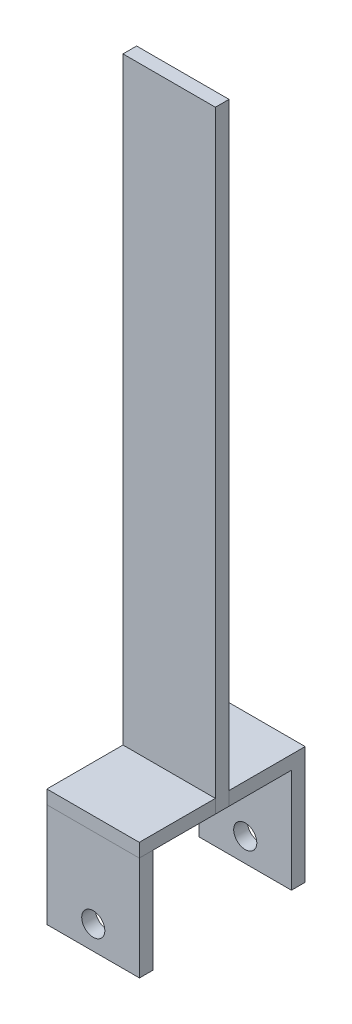
SolidWorks part; units mm, degrees
material "6063-T6"
ref_plane "Front Plane" through (0, 0, 0) normal (0, 0, 1) x (1, 0, 0)
ref_plane "Top Plane" through (0, 0, 0) normal (0, 1, 0) x (1, 0, 0)
ref_plane "Right Plane" through (0, 0, 0) normal (1, 0, 0) x (0, 0, -1)
sketch "Sketch1" plane through (0, 0, 0) normal (0, 0, 1) x (1, 0, 0)
  line L0 (-11.8389, 67.31) -> (8.4811, 67.31)
  line L1 (8.4811, 67.31) -> (8.4811, -67.31)
  line L2 (8.4811, -67.31) -> (-11.8389, -67.31)
  line L3 (-11.8389, -67.31) -> (-11.8389, 67.31)
  point P3 (-1.6789, 67.31)
  dimension "D1" = 134.62
  dimension "D2" = 20.32
  dimension "D3" = 67.31
extrude "Boss-Extrude1" add sketch "Sketch1" along normal blind 3
ref_plane "Plane1" through (0, -67.31, 0) normal (0, 1, 0) x (1, 0, 0)
sketch "Sketch2" plane through (0, -67.31, 0) normal (0, 1, 0) x (1, 0, 0)
  line L0 (-11.8389, 0) -> (-11.8389, 16.7386)
  line L1 (-11.8389, 16.7386) -> (8.4787, 16.7386)
  line L2 (8.4787, 16.7386) -> (8.4811, 0)
  line L3 (-11.8389, -19.7386) -> (-11.8389, -3)
  line L4 (-11.8389, 0) -> (-11.8389, -3)
  line L5 (8.4787, -3) -> (8.4811, -19.7386)
  line L6 (8.4787, -3) -> (8.4811, 0)
  line L7 (8.4811, -19.7386) -> (-11.8389, -19.7386)
  dimension "D1" = 16.7386
extrude "Boss-Extrude2" add sketch "Sketch2" along normal blind 3
sketch "Sketch3" plane through (0, -67.31, 0) normal (0, -1, 0) x (-1, 0, 0)
  line L0 (11.8389, 16.7386) -> (11.8389, 13.7236)
  line L1 (11.8389, 16.7386) -> (11.8389, -19.7386) construction
  line L2 (11.8389, 13.7236) -> (-8.4792, 13.7236)
  line L3 (-8.4811, 0) -> (-8.4787, 16.7386) construction
  line L4 (-8.4792, 13.7236) -> (-8.4787, 16.7386)
  line L5 (-8.4787, 16.7386) -> (11.8389, 16.7386)
  line L6 (-8.4811, -16.6772) -> (-8.4811, -19.6922)
  line L7 (-8.4811, -19.6922) -> (11.837, -19.6922)
  line L8 (11.837, -19.6922) -> (11.8366, -16.6772)
  line L9 (11.8366, -16.6772) -> (-8.4811, -16.6772)
  dimension "D1" = 3.015
  dimension "D2" = 3.015
extrude "Boss-Extrude3" add sketch "Sketch3" along normal blind 22.86
sketch "Sketch4" plane through (0, 0, -16.7386) normal (0, 0, -1) x (-1, 0, 0)
  line L0 (1.6801, -90.17) -> (1.6801, -87.5013)
  line L1 (-8.4787, -90.17) -> (11.8389, -90.17) construction
  circle A0 centre (1.6801, -84.9613) radius 2.54
  dimension "D1" = 5.08
extrude "Cut-Extrude1" cut sketch "Sketch4" against normal through all contours A0
